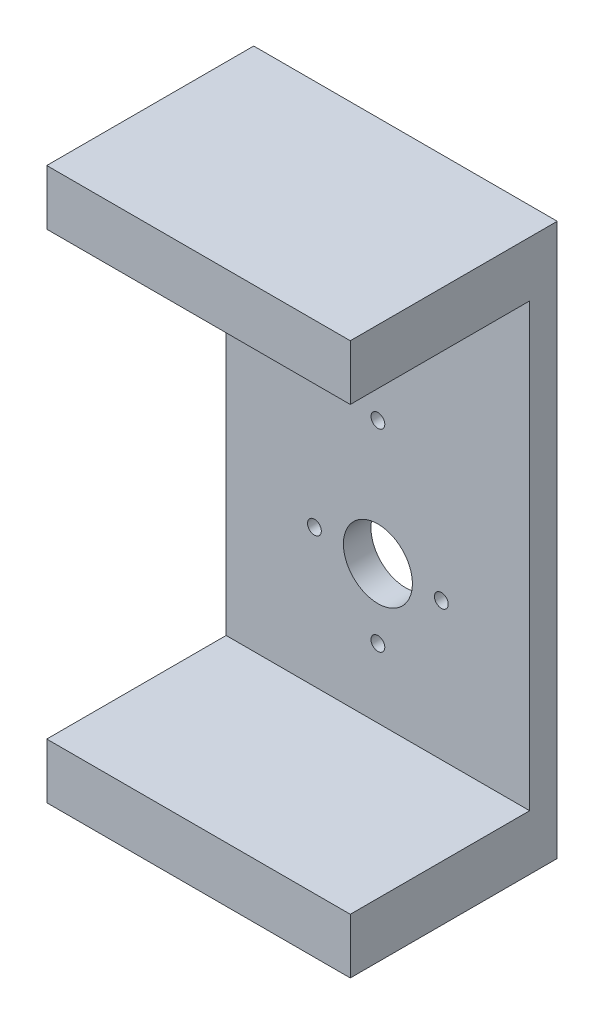
SolidWorks part; units mm, degrees
ref_plane "Front Plane" through (0, 0, 0) normal (1, 0, 0) x (0, 1, 0)
ref_plane "Top Plane" through (0, 0, 0) normal (0, 0, 1) x (0, 1, 0)
ref_plane "Right Plane" through (0, 0, 0) normal (0, 1, 0) x (-1, 0, 0)
sketch "Sketch1" plane through (0, 0, 0) normal (0, 0, 1) x (0, 1, 0)
  line L1 (-100, -55) -> (100, -55)
  line L2 (-100, -55) -> (-100, 55)
  line L3 (-100, 55) -> (100, 55)
  line L4 (100, -55) -> (100, 55)
  line L5 (-100, -55) -> (100, 55) construction
  line L6 (-100, 55) -> (100, -55) construction
  point P0 (0, 0)
  dimension "D1" = 110
  dimension "D2" = 200
extrude "Boss-Extrude1" add sketch "Sketch1" along normal blind 10
sketch "Sketch2" plane through (0, 0, 10) normal (0, 0, 1) x (1, 0, 0)
  line L0 (55, -100) -> (55, 100) construction
  line L1 (-55, 100) -> (55, 100)
  line L2 (-55, 100) -> (-55, 80)
  line L3 (-55, 80) -> (55, 80)
  line L4 (55, 100) -> (55, 80)
  line L5 (0, 0) -> (88.7154, 0) construction
  line L6 (55, -100) -> (55, -80)
  line L7 (-55, -80) -> (55, -80)
  line L8 (-55, -100) -> (-55, -80)
  line L9 (-55, -100) -> (55, -100)
  dimension "D1" = 20
extrude "Boss-Extrude2" add sketch "Sketch2" along normal blind 65
sketch "Sketch3" plane through (0, 0, 0) normal (0, 0, -1) x (1, 0, 0)
  circle A0 centre (0, 55) radius 2.5
  circle A1 centre (0, 30) radius 2.5
  circle A2 centre (0, -15) radius 2.5
  point P6 (0, 0)
  point P7 (0, 0)
  point P9 (0, 0)
  point P10 (0.0836, 30.8815)
  point P12 (0, -14.0987)
  point P13 (0, -14.2664)
  point P14 (0, 0)
  point P15 (0, 0)
  dimension "D1" = 5
  dimension "D2" = 25
  dimension "D3" = 45
  dimension "D4" = 15
sketch "Sketch4" plane through (0, 0, 0) normal (0, 0, -1) x (1, 0, 0)
  circle A1 centre (0, 30) radius 12.5
  dimension "D1" = 25
extrude "Cut-Extrude1" cut sketch "Sketch4" against normal through all
sketch "Sketch5" plane through (0, 0, 0) normal (0, 0, -1) x (1, 0, 0)
  circle A0 centre (23, 30) radius 2.5
  circle A1 centre (-23, 30) radius 2.5
  point P4 (0, 0)
  point P6 (0, 0)
  point P9 (-20.1066, 41.244)
  dimension "D1" = 5
  dimension "D2" = 23
  dimension "D3" = 23
extrude "Cut-Extrude2" cut sketch "Sketch5" against normal through all contours A0 | A1
extrude "Cut-Extrude3" cut sketch "Sketch3" against normal through all contours A2 | A0
equation "\"D2@Sketch5\"=\"D3@Sketch5\""
